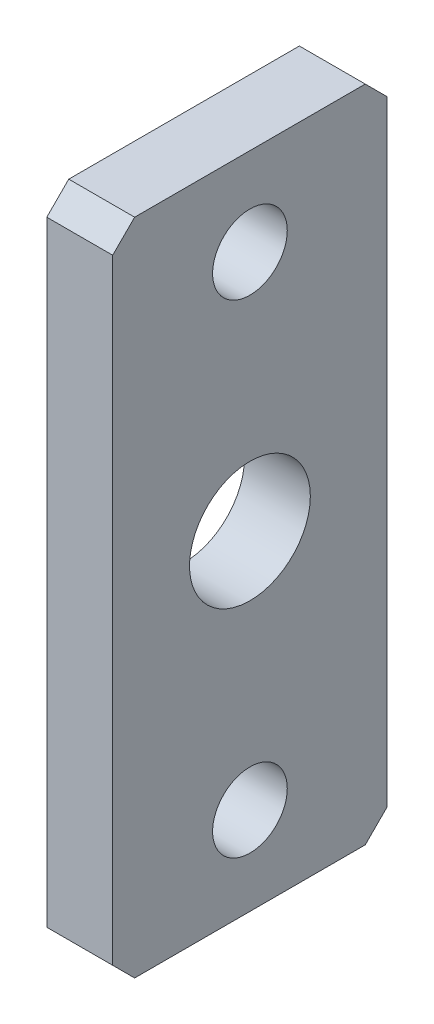
SolidWorks part; units mm, degrees
ref_plane "Front" through (0, 0, 0) normal (0, 0, 1) x (1, 0, 0)
ref_plane "Top" through (0, 0, 0) normal (0, 1, 0) x (1, 0, 0)
ref_plane "Right" through (0, 0, 0) normal (1, 0, 0) x (0, 0, -1)
sketch "Sketch1" plane through (0, 0, 0) normal (1, 0, 0) x (0, 0, -1)
  line L0 (-4.8776, 0) -> (29.3392, 0) construction
  line L2 (0, 30) -> (25, 30)
  line L3 (0, 30) -> (0, -30)
  line L4 (0, -30) -> (25, -30)
  line L5 (25, 30) -> (25, -30)
  dimension "D1" = 60
  dimension "D2" = 25
extrude "Boss-Extrude1" add sketch "Sketch1" against normal blind 6
hole_wizard "Ø11.0 (11) Diameter Hole1" positions "Sketch3" profile "Sketch4" hole size "Ø11.0" standard "JIS" end condition through all
sketch "Sketch3" plane through (0, 0, 0) normal (1, 0, 0) x (0, 0, -1)
  line L3 (-5.9841, 0) -> (27.3703, 0) construction
  point P0 (12.5, 0)
  dimension "D1" = 12.5
sketch "Sketch4" plane through (0, 0, -12.5) normal (0, 1, 0) x (0, 0, -1)
  line L0 (0, 0) -> (0, 6)
  line L1 (0, 6) -> (5.5, 6)
  line L2 (5.5, 6) -> (5.5, 0)
  line L5 (5.5, 0) -> (0, 0)
  line L11 (0, -6.35) -> (0, 107.95) construction
  dimension "Thru Hole Dia." = 11
  dimension "Thru Hole Depth" = 6
hole_wizard "M8x1.25 Tapped Hole1" positions "Sketch6" profile "Sketch5" tap size "M8x1.25" standard "JIS" end condition through all
sketch "Sketch6" plane through (0, 0, 0) normal (1, 0, 0) x (0, 0, -1)
  line L0 (-2.3903, 0) -> (27.3903, 0) construction
  point P0 (12.5, 22)
  point P8 (12.5, -22)
  dimension "D1" = 44
  dimension "D2" = 12.5
sketch "Sketch5" plane through (0, 22, -12.5) normal (0, 1, 0) x (0, 0, -1)
  line L0 (0, 0) -> (0, 6)
  line L1 (0, 6) -> (3.4, 6)
  line L2 (3.4, 6) -> (3.4, 0)
  line L5 (3.4, 0) -> (0, 0)
  line L11 (0, -6.35) -> (0, 107.95) construction
  dimension "Thru Tap Drill Dia." = 6.8
  dimension "Thru Tap Drill Depth" = 6
cosmetic thread "Hole Thread1" parameters "D2"=8
cosmetic thread "Hole Thread2" parameters "D2"=8
chamfer "Chamfer1" distance 2 angle 45 4 edges at (-3, 30, -25) (-3, -30, -25) (-3, -30, 0) (-3, 30, 0)
